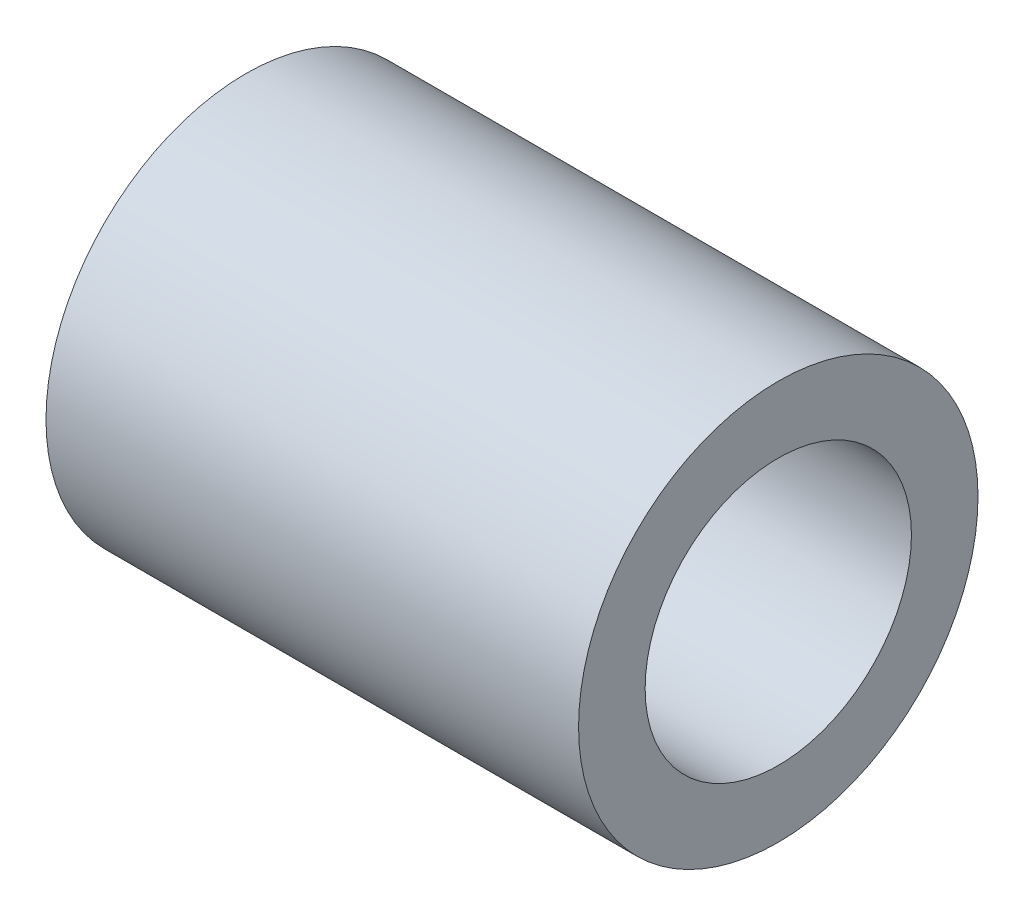
SolidWorks part; units mm, degrees
ref_plane "Front Plane" through (0, 0, 0) normal (0, 0, 1) x (1, 0, 0)
ref_plane "Top Plane" through (0, 0, 0) normal (0, 1, 0) x (1, 0, 0)
ref_plane "Right Plane" through (0, 0, 0) normal (1, 0, 0) x (0, 0, -1)
sketch "Sketch1" plane through (0, 0, 0) normal (1, 0, 0) x (0, 0, -1)
  circle A0 centre (0, 0) radius 25
  circle A1 centre (0, 0) radius 37.5
  dimension "D1" = 75
  dimension "D2" = 50
extrude "Boss-Extrude1" add sketch "Sketch1" along normal mid plane 100
